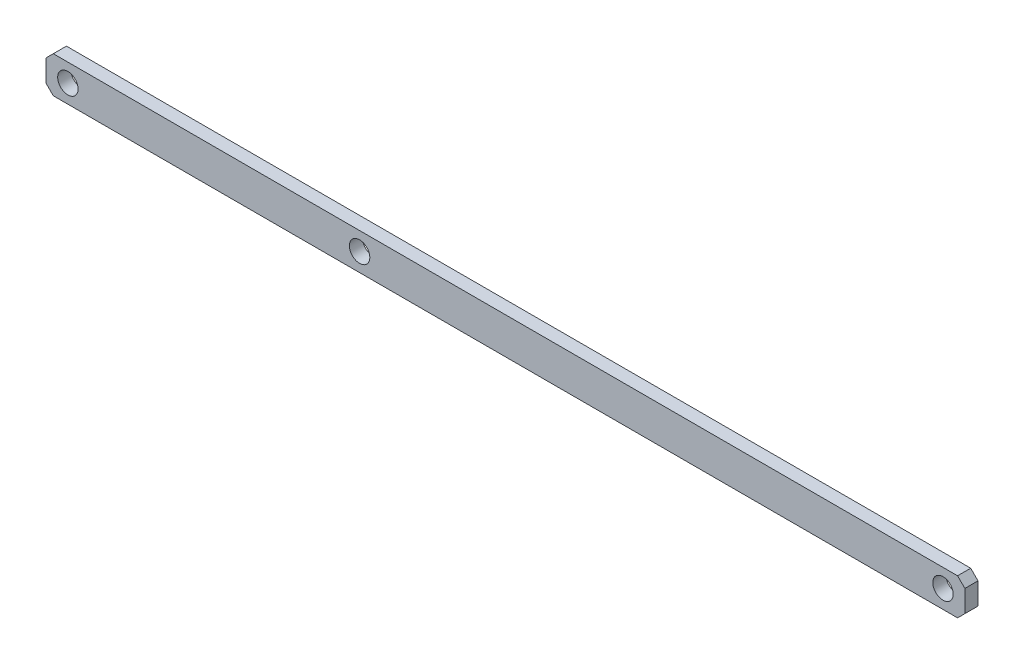
SolidWorks part; units mm, degrees
ref_plane "前基準面" through (0, 0, 0) normal (0, 0, 1) x (1, 0, 0)
ref_plane "上基準面" through (0, 0, 0) normal (0, 1, 0) x (1, 0, 0)
ref_plane "右基準面" through (0, 0, 0) normal (1, 0, 0) x (0, 0, -1)
sketch "草圖1" plane through (0, 0, 0) normal (0, 0, 1) x (1, 0, 0)
  line L0 (-215, 7.5) -> (-210, 12.5)
  line L1 (-210, -12.5) -> (410, -12.5)
  line L2 (-215, -7.5) -> (-215, 7.5)
  line L3 (-210, 12.5) -> (410, 12.5)
  line L4 (415, -7.5) -> (415, 7.5)
  line L5 (-210, -12.5) -> (-215, -7.5)
  line L6 (410, -12.5) -> (415, -7.5)
  line L7 (410, 12.5) -> (415, 7.5)
  line L8 (-262.3841, 0) -> (506.953, 0) construction
  circle A0 centre (0, 0) radius 7
  circle A1 centre (400, 0) radius 7
  circle A2 centre (-200, 0) radius 7
  point P0 (-215, -12.5)
  point P1 (415, 12.5)
  point P2 (-215, 12.5)
  point P3 (415, -12.5)
  point P21 (415, 0)
  point P22 (0, 0)
  point P23 (0, 0)
  point P24 (0, 0)
  dimension "D1" = 14
  dimension "D3" = 15
  dimension "D4" = 15
  dimension "D2" = 400
  dimension "D5" = 25
  dimension "200" = 200
extrude "填料-伸長1" add sketch "草圖1" along normal mid plane 9
